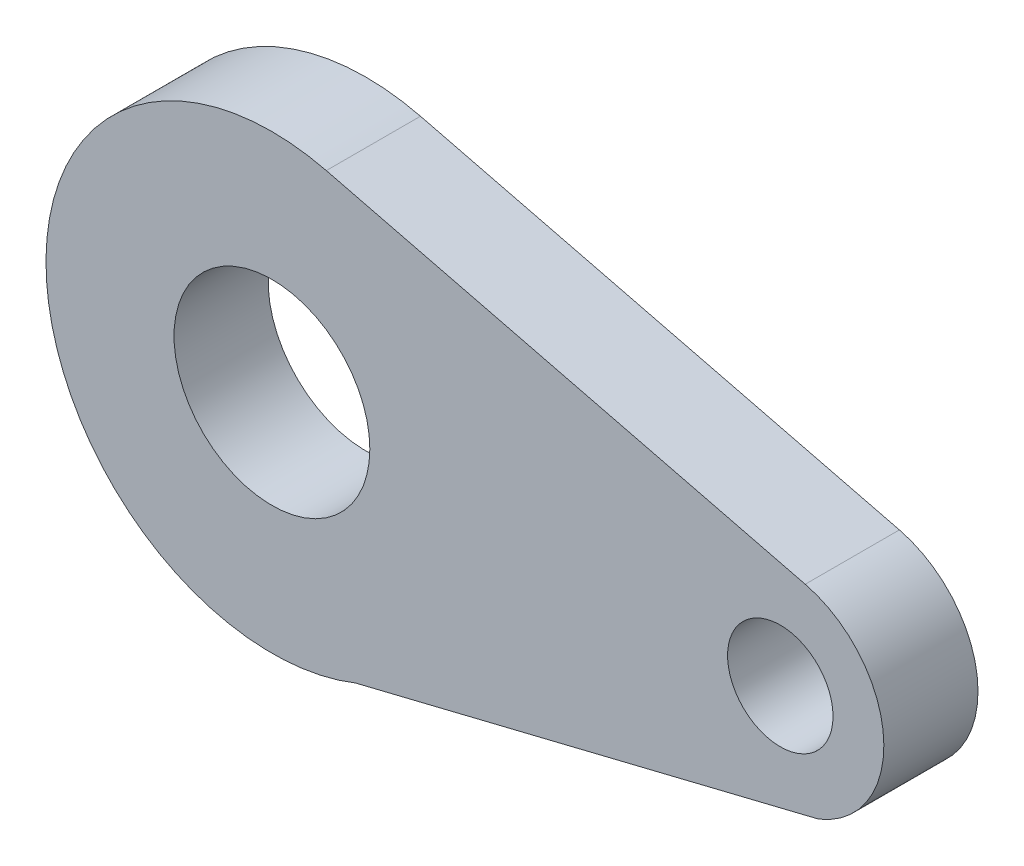
SolidWorks part; units mm, degrees
ref_plane "前基準面" through (0, 0, 0) normal (0, 0, 1) x (1, 0, 0)
ref_plane "上基準面" through (0, 0, 0) normal (0, 1, 0) x (1, 0, 0)
ref_plane "右基準面" through (0, 0, 0) normal (1, 0, 0) x (0, 0, -1)
sketch "草圖1" plane through (0, 0, 0) normal (0, 0, 1) x (1, 0, 0)
  line L0 (1.4444, 5.8235) -> (14.162, 2.6691)
  line L2 (0, 0) -> (13.5, 0) construction
  line L3 (14.5185, -2.5544) -> (2.2222, -5.5733)
  circle A0 centre (0, 0) radius 2.6
  arc A1 (1.4444, 5.8235) -> (2.2222, -5.5733) centre (0, 0) ccw
  circle A2 centre (13.5, 0) radius 1.4
  arc A3 (14.5185, -2.5544) -> (14.162, 2.6691) centre (13.5, 0) ccw
  dimension "D2" = 5.2
  dimension "D3" = 12
  dimension "D4" = 2.8
  dimension "D5" = 5.5
  dimension "D6" = 13.5
extrude "填料-伸長1" add sketch "草圖1" along normal blind 2.5
